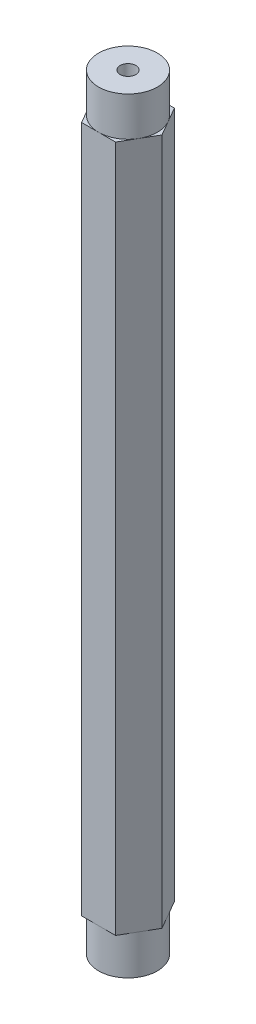
SolidWorks part; units mm, degrees
material "Alum Plate"
ref_plane "Front Plane" through (0, 0, 0) normal (0, 0, 1) x (1, 0, 0)
ref_plane "Top Plane" through (0, 0, 0) normal (0, 1, 0) x (1, 0, 0)
ref_plane "Right Plane" through (0, 0, 0) normal (1, 0, 0) x (0, 0, -1)
other "Bounding Box"
ref_plane "Default Plane" through (-8.9266, -12.7485, 0) normal (-0.1736, 0.9848, 0) x (0.9848, 0.1736, 0)
sketch "Sketch1" plane through (0, 0, 0) normal (0, 1, 0) x (1, 0, 0)
  line L1 (1.3748, -2.3812) -> (2.7496, 0)
  line L2 (2.7496, 0) -> (1.3748, 2.3813)
  line L3 (1.3748, 2.3813) -> (-1.3748, 2.3813)
  line L4 (-1.3748, 2.3813) -> (-2.7496, 0)
  line L5 (-2.7496, 0) -> (-1.3748, -2.3812)
  line L6 (-1.3748, -2.3812) -> (1.3748, -2.3812)
  circle A0 centre (0, 0) radius 2.3813 construction
  circle A1 centre (0, 0) radius 0.635
  dimension "D2" = 1.27
  dimension "D1" = 4.7625
extrude "Boss-Extrude1" add sketch "Sketch1" along normal mid plane 55.626
sketch "Sketch2" plane through (0, 27.813, 0) normal (0, 1, 0) x (1, 0, 0)
  circle A0 centre (0, 0) radius 2.3813
  circle A1 centre (0, 0) radius 0.635 construction
  circle A2 centre (0, 0) radius 0.635
  dimension "D1" = 4.7625
extrude "Boss-Extrude2" add sketch "Sketch2" along normal blind 3.175
sketch "Sketch3" plane through (0, -27.813, 0) normal (0, -1, 0) x (1, 0, 0)
  circle A0 centre (0, 0) radius 0.635 construction
  circle A1 centre (0, 0) radius 0.635
  circle A2 centre (0, 0) radius 2.3813
  dimension "D1" = 4.7625
extrude "Boss-Extrude3" add sketch "Sketch3" along normal blind 3.175
